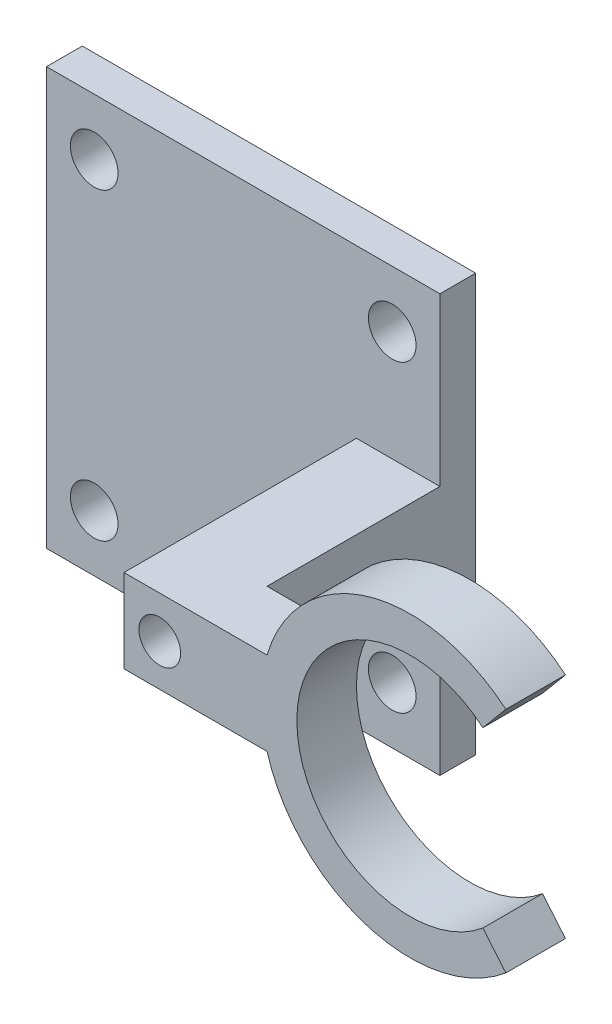
SolidWorks part; units mm, degrees
ref_plane "Plano frontal" through (0, 0, 0) normal (0, 0, 1) x (1, 0, 0)
ref_plane "Plano superior" through (0, 0, 0) normal (0, 1, 0) x (1, 0, 0)
ref_plane "Plano direito" through (0, 0, 0) normal (1, 0, 0) x (0, 0, -1)
sketch "Esboço1" plane through (0, 0, 0) normal (0, 0, 1) x (1, 0, 0)
  line L0 (7.0707, 8.4265) -> (0, 0) construction
  line L1 (0, 0) -> (7.0707, -8.4265) construction
  line L2 (-11, 0) -> (-19.8171, 0) construction
  arc A0 (7.0707, 8.4265) -> (7.0707, -8.4265) centre (0, 0) ccw
  point P6 (0, 0)
  dimension "D1" = 11
  dimension "D2" = 100
sketch "Esboço14" plane through (0, 0, 0) normal (0, 1, 0) x (1, 0, 0)
  line L0 (-12, 2.5) -> (-17, 2.5)
  line L1 (-24, 17) -> (-50, 17)
  line L2 (-50, 20) -> (-17, 20)
  line L3 (-50, 17) -> (-50, 20)
  line L4 (-17, 2.5) -> (-17, 20)
  line L6 (-12, -2.5) -> (-24, -2.5)
  line L7 (-12, 2.5) -> (-12, -2.5)
  line L8 (-24, -2.5) -> (-24, 17)
  point P3 (-12, 0)
  dimension "D1" = 33
  dimension "D2" = 5
  dimension "D3" = 20
  dimension "D4" = 12
  dimension "D5" = 7
  dimension "D6" = 3
  dimension "D7" = 12
extrude "Ressalto-extrusão1" add sketch "Esboço14" along normal mid plane 7
sketch "Esboço15" plane through (0, 0, -20) normal (0, 0, -1) x (-1, 0, 0)
  line L1 (17, 17.5) -> (50, 17.5)
  line L2 (17, 17.5) -> (17, -17.5)
  line L3 (17, -17.5) -> (50, -17.5)
  line L4 (50, 17.5) -> (50, -17.5)
  line L6 (17, 0) -> (50, 0) construction
  line L7 (33.5, 6.952) -> (33.5, -7.5) construction
  line L8 (17, 3.5) -> (17, -3.5) construction
  line L9 (50, 3.5) -> (50, -3.5) construction
  circle A0 centre (21, 12.75) radius 2
  circle A1 centre (21, -12.75) radius 2
  circle A2 centre (46, -12.75) radius 2
  circle A3 centre (46, 12.75) radius 2
  point P5 (24, 0)
  point P6 (50, 0)
  point P7 (24, 0)
  point P8 (17, 0)
  point P9 (17, 0)
  point P22 (-9, 0)
  point P23 (-9, 0)
  point P26 (33.5, -17.5)
  line M4 (17, -3.5) -> (50, -3.5)
  line M6 (50, 3.5) -> (17, 3.5)
  line M14 (50, -3.5) -> (50, 3.5)
  line M15 (17, 3.5) -> (17, -3.5)
  dimension "D3" = 4
  dimension "D1" = 35
  dimension "D2" = 25.5
  dimension "D4" = 4
extrude "Ressalto-extrusão2" add sketch "Esboço15" against normal up to surface (3 mm away) contours L4 L2 L3 A1 A2 M4 | L4 L1 L2 A0 A3 M6 | M15 M4 M14 M6 up to face at (-37, 0, -17)
sketch "Esboço16" plane through (0, 0, 2.5) normal (0, 0, 1) x (1, 0, 0)
  line L0 (-24, 3.5) -> (-18, -3.5) construction
  line L1 (-24, -3.5) -> (-12, -3.5) construction
  circle A0 centre (-21, 0) radius 1.75
  dimension "D1" = 3.5
extrude "Corte-extrusão1" cut sketch "Esboço16" against normal through all
sketch3d "3DSketch2"
  line L0 (0, 0, 0) -> (7.0707, -8.4265, 0) construction
  line L1 (8.0348, -9.5756, 2.5) -> (6.1065, -7.2774, 2.5)
  line L2 (6.1065, -7.2774, 2.5) -> (6.1065, -7.2774, -2.5)
  line L3 (6.1065, -7.2774, -2.5) -> (8.0348, -9.5756, -2.5)
  line L4 (8.0348, -9.5756, -2.5) -> (8.0348, -9.5756, 2.5)
  line L5 (-12, -3.5, 2.5) -> (-12, -3.5, -2.5) construction
  point P4 (6.1065, -7.2774, 0)
  point P10 (7.0707, -8.4265, 0)
  dimension "D3" = 3
  dimension "D4" = 1.5
sweep "Varredura1" add profiles "3DSketch2" path "Esboço1"
